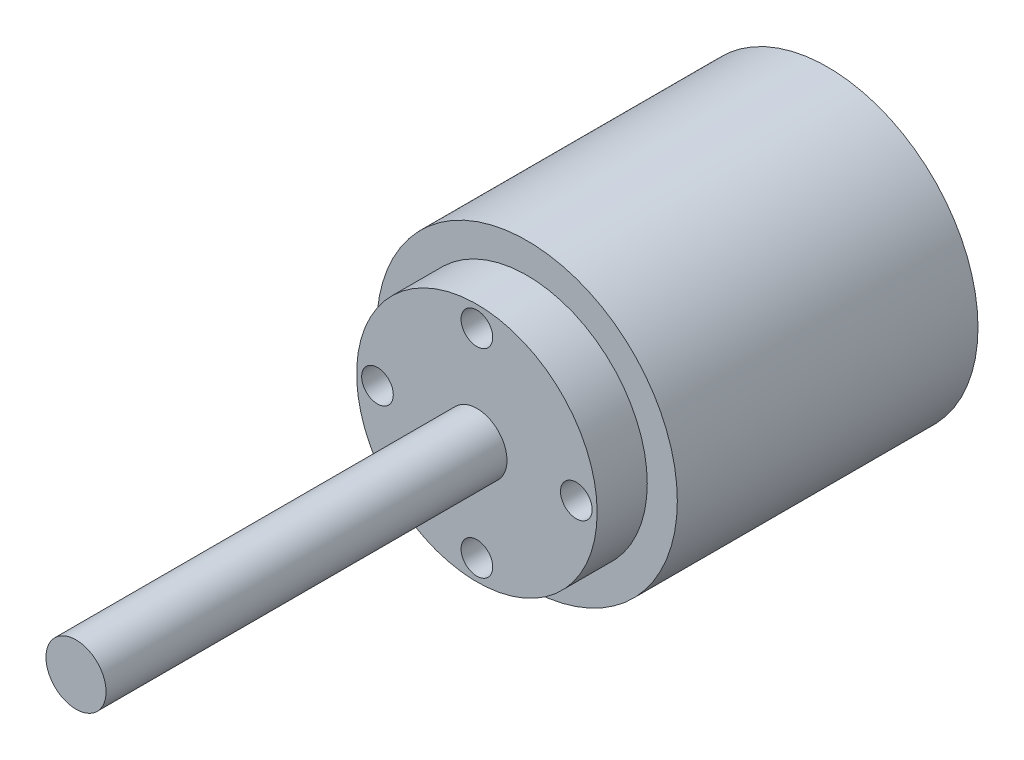
SolidWorks part; units mm, degrees
ref_plane "Front Plane" through (0, 0, 0) normal (0, 0, 1) x (1, 0, 0)
ref_plane "Top Plane" through (0, 0, 0) normal (0, 1, 0) x (1, 0, 0)
ref_plane "Right Plane" through (0, 0, 0) normal (1, 0, 0) x (0, 0, -1)
sketch "Sketch1" plane through (0, 0, 0) normal (0, 0, 1) x (1, 0, 0)
  circle A0 centre (5.1787, -6.9251) radius 15
extrude "Boss-Extrude1" add sketch "Sketch1" along normal blind 30
sketch "Sketch2" plane through (0, 0, 30) normal (0, 0, 1) x (1, 0, 0)
  circle A0 centre (5.1787, -6.9251) radius 12
extrude "Boss-Extrude2" add sketch "Sketch2" along normal blind 5
sketch "Sketch4" plane through (0, 0, 35) normal (0, 0, 1) x (1, 0, 0)
  circle A1 centre (5.1787, 2.9956) radius 1.5793
  circle A2 centre (15.0994, -6.9251) radius 1.5793
  circle A3 centre (5.1787, -16.8458) radius 1.5793
  circle A4 centre (-4.742, -6.9251) radius 1.5793
  point P14 (5.1787, -6.9251)
  dimension "D1" = 4
extrude "Cut-Extrude3" cut sketch "Sketch4" against normal blind 3
sketch "Sketch5" plane through (0, 0, 35) normal (0, 0, 1) x (1, 0, 0)
  circle A0 centre (5.1787, -6.9251) radius 3
extrude "Boss-Extrude3" add sketch "Sketch5" along normal blind 40
